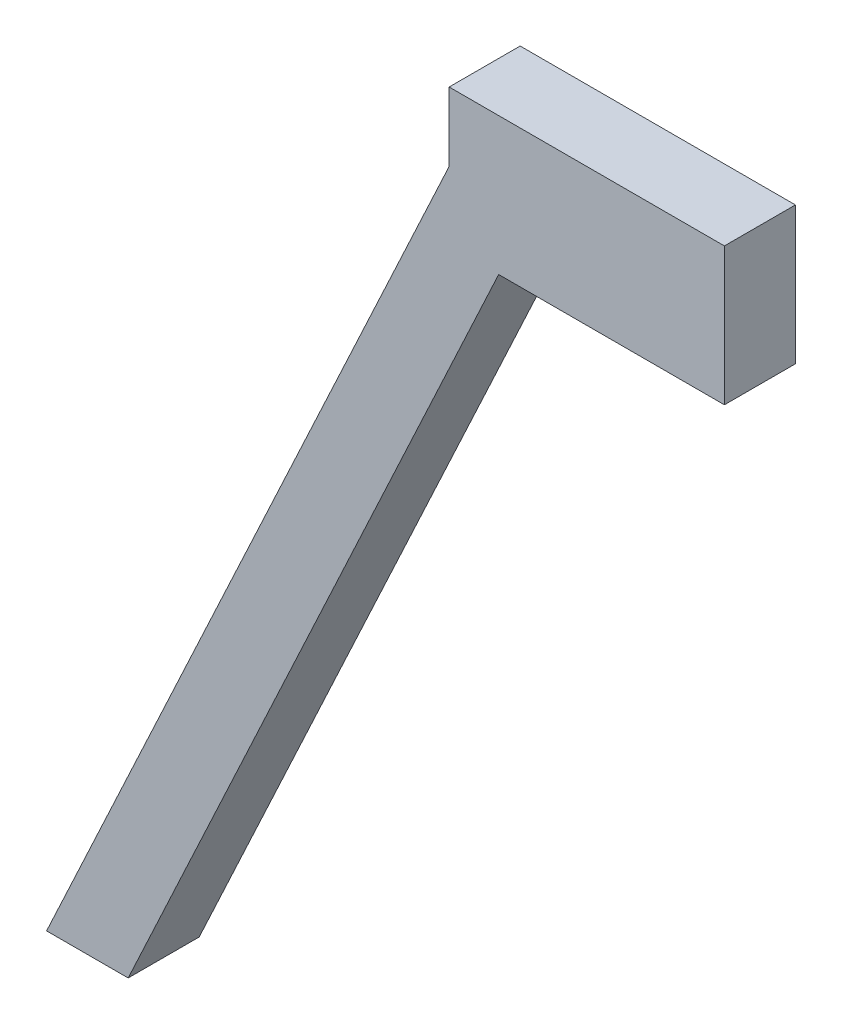
SolidWorks part; units mm, degrees
ref_plane "Front Plane" through (0, 0, 0) normal (0, 0, 1) x (1, 0, 0)
ref_plane "Top Plane" through (0, 0, 0) normal (0, 1, 0) x (1, 0, 0)
ref_plane "Right Plane" through (0, 0, 0) normal (1, 0, 0) x (0, 0, -1)
sketch "Sketch2" plane through (0, 0, 0) normal (0, 0, 1) x (1, 0, 0)
  line L0 (14.5398, 82.0991) -> (-41.4169, -37.9006)
  line L1 (7.3452, 102.0991) -> (47.3452, 102.0991)
  line L2 (7.3452, 102.0991) -> (7.3452, 92.0991)
  line L3 (14.5398, 82.0991) -> (47.3452, 82.0991)
  line L4 (47.3452, 102.0991) -> (47.3452, 82.0991)
  line L5 (-41.4169, -37.9006) -> (-51.1568, -33.3589)
  line L6 (-51.1568, -33.3589) -> (7.3452, 92.0991)
  dimension "D1" = 40
  dimension "D2" = 20
  dimension "D3" = 115
  dimension "D4" = 90
  dimension "D5" = 90
extrude "Boss-Extrude1" add sketch "Sketch2" along normal blind 10 and the other way blind 0.3183
sketch "Sketch3" plane through (0, 82.0991, 0) normal (0, -1, 0) x (1, 0, 0)
  line L0 (37.2232, 10) -> (37.2232, 5)
  line L1 (14.5398, 10) -> (47.3452, 10) construction
  circle A1 centre (37.2232, 5) radius 3
extrude "Cut-Extrude1" cut sketch "Sketch3" against normal blind 5
sketch "Sketch4" plane through (0, 0, -0.3183) normal (0, 0, -1) x (-1, 0, 0)
  line L0 (51.1568, -33.3589) -> (39.2991, -33.3589)
  line L1 (41.4169, -37.9006) -> (-14.5398, 82.0991) construction
  line L2 (-14.5398, 82.0991) -> (-47.3452, 82.0991) construction
  line L3 (39.2991, -33.3589) -> (41.4169, -37.9006)
  line L4 (41.4169, -37.9006) -> (51.1568, -33.3589)
extrude "Cut-Extrude2" cut sketch "Sketch4" against normal blind 15
